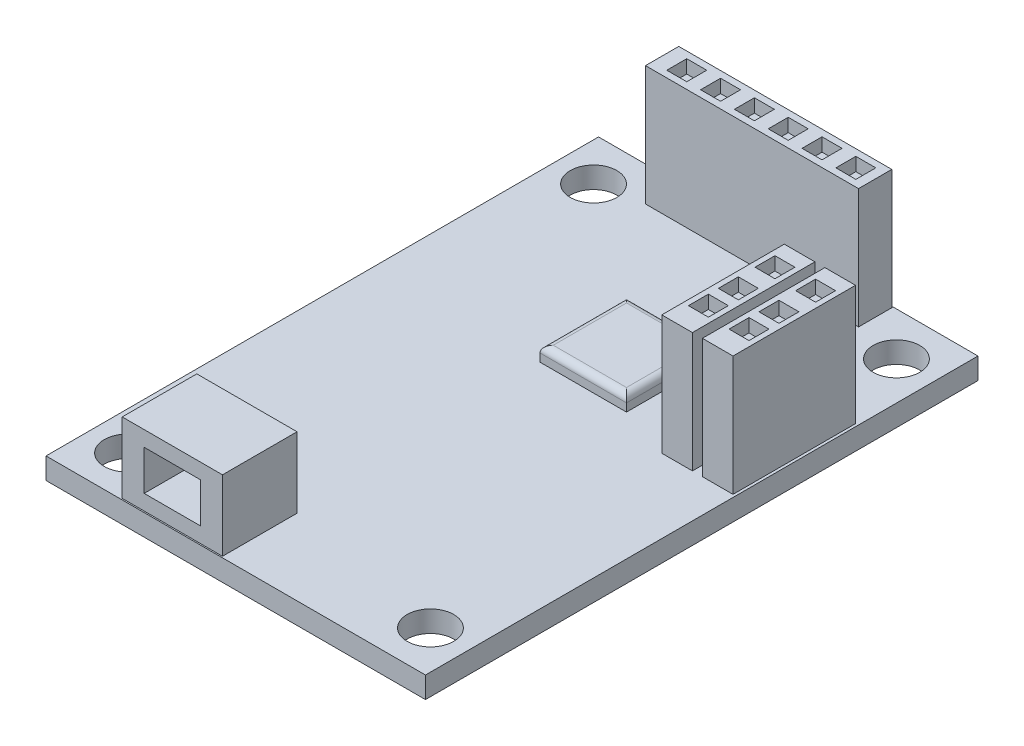
SolidWorks part; units mm, degrees
ref_plane "Front Plane" through (0, 0, 0) normal (0, 0, 1) x (1, 0, 0)
ref_plane "Top Plane" through (0, 0, 0) normal (0, 1, 0) x (1, 0, 0)
ref_plane "Right Plane" through (0, 0, 0) normal (1, 0, 0) x (0, 0, -1)
sketch "Sketch1" plane through (0, 0, 0) normal (0, 1, 0) x (1, 0, 0)
  line L0 (-14.25, 0) -> (14.25, 0) construction
  line L1 (-14.25, -20.75) -> (14.25, -20.75)
  line L2 (-14.25, -20.75) -> (-14.25, 20.75)
  line L3 (-14.25, 20.75) -> (14.25, 20.75)
  line L4 (14.25, -20.75) -> (14.25, 20.75)
  line L5 (-14.25, -20.75) -> (14.25, 20.75) construction
  line L6 (-14.25, 20.75) -> (14.25, -20.75) construction
  line L7 (0, 20.75) -> (0, -20.75) construction
  circle A0 centre (11.375, 17.5) radius 1.75
  circle A1 centre (-11.375, 17.5) radius 1.75
  circle A2 centre (-11.375, -17.5) radius 1.75
  circle A3 centre (11.375, -17.5) radius 1.75
  point P0 (0, 0)
  dimension "D3" = 3.5
  dimension "D1" = 28.5
  dimension "D2" = 41.5
  dimension "D4" = 11.375
  dimension "D5" = 17.5
extrude "Boss-Extrude1" add sketch "Sketch1" along normal blind 1.6
sketch "Sketch2" plane through (0, 1.6, 0) normal (0, 1, 0) x (1, 0, 0)
  line L0 (11.375, 17.5) -> (11.375, 9.0803) construction
  line L1 (11.375, 9.0803) -> (11.375, 7.9813) construction
  line L2 (11, 11.75) -> (8.7, 2.55) construction
  line L3 (11.75, 11.75) -> (14.05, 11.75)
  line L4 (11.75, 11.75) -> (11.75, 2.55)
  line L5 (11.75, 2.55) -> (14.05, 2.55)
  line L6 (14.05, 11.75) -> (14.05, 2.55)
  line L7 (11.75, 11.75) -> (14.05, 2.55) construction
  line L8 (11.75, 2.55) -> (14.05, 11.75) construction
  line L9 (8.7, 11.75) -> (8.7, 2.55)
  line L10 (11, 2.55) -> (8.7, 2.55)
  line L11 (11, 11.75) -> (11, 2.55)
  line L12 (11, 11.75) -> (8.7, 11.75)
  line L13 (14.25, 20.75) -> (-14.25, 20.75) construction
  line L14 (7.875, 20.65) -> (-8.125, 20.65)
  line L15 (7.875, 20.65) -> (7.875, 18.15)
  line L16 (7.875, 18.15) -> (-8.125, 18.15)
  line L17 (-8.125, 20.65) -> (-8.125, 18.15)
  line L18 (7.875, 20.65) -> (-8.125, 18.15) construction
  line L19 (7.875, 18.15) -> (-8.125, 20.65) construction
  point P4 (12.9, 7.15)
  point P13 (9.85, 7.15)
  point P14 (-0.125, 19.4)
  dimension "D1" = 5.75
  dimension "D2" = 2.3
  dimension "D3" = 9.2
  dimension "D4" = 0.375
  dimension "D5" = 16
  dimension "D6" = 2.5
  dimension "D7" = 0.1
  dimension "D8" = 3.5
extrude "Boss-Extrude2" add sketch "Sketch2" along normal blind 9
sketch "Sketch3" plane through (0, 10.6, 0) normal (0, 1, 0) x (1, 0, 0)
  line L0 (11.75, 11.75) -> (14.05, 2.55) construction
  line L1 (11.75, 11.75) -> (14.05, 11.75) construction
  line L2 (11.75, 11.75) -> (11.75, 2.55) construction
  line L3 (11.75, 2.55) -> (14.05, 2.55) construction
  line L4 (14.05, 11.75) -> (14.05, 2.55) construction
  line L5 (14.05, 11.75) -> (11.75, 2.55) construction
  line L6 (11.75, 11.75) -> (11, 11.75) construction
  line L7 (12.15, 6.4) -> (13.65, 6.4)
  line L8 (12.15, 6.4) -> (12.15, 7.9)
  line L9 (12.15, 7.9) -> (13.65, 7.9)
  line L10 (13.65, 6.4) -> (13.65, 7.9)
  line L11 (12.15, 6.4) -> (13.65, 7.9) construction
  line L12 (12.15, 7.9) -> (13.65, 6.4) construction
  line L13 (11.375, 11.75) -> (11.375, 2.8) construction
  line L14 (12.15, 10.65) -> (13.65, 10.65)
  line L15 (12.15, 9.15) -> (12.15, 10.65)
  line L16 (13.65, 9.15) -> (13.65, 10.65)
  line L17 (12.15, 9.15) -> (13.65, 9.15)
  line L18 (13.65, 4.15) -> (13.65, 5.65)
  line L19 (12.15, 5.65) -> (13.65, 5.65)
  line L20 (12.15, 4.15) -> (12.15, 5.65)
  line L21 (12.15, 4.15) -> (13.65, 4.15)
  line L22 (9.1, 4.15) -> (9.1, 5.65)
  line L23 (10.6, 4.15) -> (9.1, 4.15)
  line L24 (10.6, 4.15) -> (10.6, 5.65)
  line L25 (10.6, 5.65) -> (9.1, 5.65)
  line L26 (10.6, 6.4) -> (9.1, 6.4)
  line L27 (9.1, 6.4) -> (9.1, 7.9)
  line L28 (10.6, 6.4) -> (10.6, 7.9)
  line L29 (10.6, 7.9) -> (9.1, 7.9)
  line L30 (10.6, 9.15) -> (9.1, 9.15)
  line L31 (9.1, 9.15) -> (9.1, 10.65)
  line L32 (10.6, 9.15) -> (10.6, 10.65)
  line L33 (10.6, 10.65) -> (9.1, 10.65)
  line L34 (-8.125, 20.65) -> (7.875, 18.15) construction
  line L35 (7.875, 20.65) -> (-8.125, 18.15) construction
  line L36 (7.875, 18.15) -> (7.875, 20.65) construction
  line L37 (5.675, 20.15) -> (7.175, 20.15)
  line L38 (5.675, 20.15) -> (5.675, 18.65)
  line L39 (5.675, 18.65) -> (7.175, 18.65)
  line L40 (7.175, 20.15) -> (7.175, 18.65)
  line L41 (5.675, 20.15) -> (7.175, 18.65) construction
  line L42 (5.675, 18.65) -> (7.175, 20.15) construction
  line L43 (3.135, 20.15) -> (4.635, 20.15)
  line L44 (3.135, 20.15) -> (3.135, 18.65)
  line L45 (3.135, 18.65) -> (4.635, 18.65)
  line L46 (4.635, 20.15) -> (4.635, 18.65)
  line L47 (0.595, 20.15) -> (2.095, 20.15)
  line L48 (0.595, 20.15) -> (0.595, 18.65)
  line L49 (0.595, 18.65) -> (2.095, 18.65)
  line L50 (2.095, 20.15) -> (2.095, 18.65)
  line L51 (-1.945, 20.15) -> (-0.445, 20.15)
  line L52 (-1.945, 20.15) -> (-1.945, 18.65)
  line L53 (-1.945, 18.65) -> (-0.445, 18.65)
  line L54 (-0.445, 20.15) -> (-0.445, 18.65)
  line L55 (-4.485, 20.15) -> (-2.985, 20.15)
  line L56 (-4.485, 20.15) -> (-4.485, 18.65)
  line L57 (-4.485, 18.65) -> (-2.985, 18.65)
  line L58 (-2.985, 20.15) -> (-2.985, 18.65)
  line L59 (-7.025, 20.15) -> (-5.525, 20.15)
  line L60 (-7.025, 20.15) -> (-7.025, 18.65)
  line L61 (-7.025, 18.65) -> (-5.525, 18.65)
  line L62 (-5.525, 20.15) -> (-5.525, 18.65)
  point P6 (12.9, 7.15)
  point P43 (6.425, 19.4)
  point P48 (-0.125, 19.4)
  dimension "D1" = 1.5
  dimension "D2" = 1.5
  dimension "D5" = 1.5
  dimension "D6" = 1.5
  dimension "D7" = 0.7
  dimension "D3" = 2
  dimension "D4" = 2
  dimension "D8" = 6
extrude "Cut-Extrude1" cut sketch "Sketch3" against normal blind 1
sketch "Sketch4" plane through (0, 1.6, 0) normal (0, 1, 0) x (1, 0, 0)
  line L0 (8.7, 7.15) -> (-7.0033, 7.15) construction
  line L1 (8.7, 11.75) -> (8.7, 2.55) construction
  line L3 (-1.8, 10.4) -> (4.7, 10.4)
  line L4 (-1.8, 10.4) -> (-1.8, 3.9)
  line L5 (-1.8, 3.9) -> (4.7, 3.9)
  line L6 (4.7, 10.4) -> (4.7, 3.9)
  line L7 (-1.8, 10.4) -> (4.7, 3.9) construction
  line L8 (-1.8, 3.9) -> (4.7, 10.4) construction
  point P4 (1.45, 7.15)
  dimension "D1" = 6.5
  dimension "D2" = 6.5
  dimension "D3" = 4
extrude "Boss-Extrude3" add sketch "Sketch4" along normal blind 1.1
fillet "Fillet1" radius 0.5 4 edges at (1.45, 2.7, -10.4) (4.7, 2.7, -7.15) (1.45, 2.7, -3.9) (-1.8, 2.7, -7.15)
sketch "Sketch5" plane through (0, 1.6, 0) normal (0, 1, 0) x (1, 0, 0)
  line L0 (-14.25, -20.75) -> (14.25, -20.75) construction
  line L1 (-8.625, -20.65) -> (-1.095, -20.65)
  line L2 (-8.625, -20.65) -> (-8.625, -15.05)
  line L3 (-8.625, -15.05) -> (-1.095, -15.05)
  line L4 (-1.095, -20.65) -> (-1.095, -15.05)
  line L5 (-8.625, -20.65) -> (-1.095, -15.05) construction
  line L6 (-8.625, -15.05) -> (-1.095, -20.65) construction
  point P0 (-11.375, -17.5)
  point P1 (-4.86, -17.85)
  dimension "D1" = 0.1
  dimension "D2" = 7.53
  dimension "D3" = 2.75
  dimension "D4" = 5.6
extrude "Boss-Extrude4" add sketch "Sketch5" along normal blind 5.3
sketch "Sketch6" plane through (0, 0, 20.65) normal (0, 0, 1) x (1, 0, 0)
  line L0 (-8.625, 6.9) -> (-8.3656, 6.6135) construction
  line L1 (-8.625, 6.9) -> (-1.095, 6.9) construction
  line L2 (-8.625, 6.9) -> (-8.625, 1.6) construction
  line L3 (-8.625, 1.6) -> (-1.095, 1.6) construction
  line L4 (-1.095, 6.9) -> (-1.095, 1.6) construction
  line L5 (-1.095, 1.6) -> (-8.625, 6.9) construction
  line L6 (-1.095, 6.9) -> (-8.625, 1.6) construction
  line L8 (-6.975, 2.75) -> (-2.745, 2.75)
  line L9 (-6.975, 2.75) -> (-6.975, 5.75)
  line L10 (-6.975, 5.75) -> (-2.745, 5.75)
  line L11 (-2.745, 2.75) -> (-2.745, 5.75)
  line L12 (-6.975, 2.75) -> (-2.745, 5.75) construction
  line L13 (-6.975, 5.75) -> (-2.745, 2.75) construction
  point P6 (-4.86, 4.25)
  dimension "D1" = 4.23
  dimension "D2" = 3
extrude "Cut-Extrude2" cut sketch "Sketch6" against normal blind 4.5
